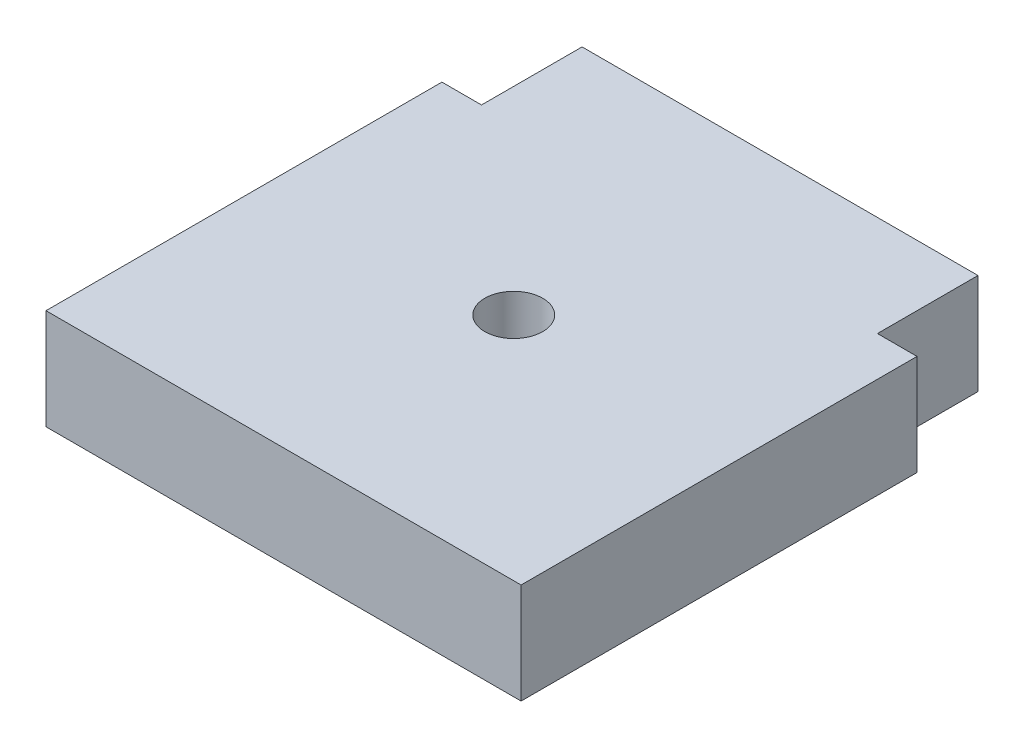
SolidWorks part; units mm, degrees
ref_plane "Front Plane" through (0, 0, 0) normal (0, 0, 1) x (1, 0, 0)
ref_plane "Top Plane" through (0, 0, 0) normal (0, 1, 0) x (1, 0, 0)
ref_plane "Right Plane" through (0, 0, 0) normal (1, 0, 0) x (0, 0, -1)
sketch "Sketch1" plane through (0, 0, 0) normal (0, 1, 0) x (1, 0, 0)
  line L0 (-12.5, 12.5) -> (-15, 12.5)
  line L1 (15, -12.5) -> (-15, -12.5)
  line L2 (15, -12.5) -> (15, 12.5)
  line L3 (15, 12.5) -> (12.5, 12.5)
  line L4 (-15, -12.5) -> (-15, 12.5)
  line L5 (15, -12.5) -> (-15, 12.5) construction
  line L6 (15, 12.5) -> (-15, -12.5) construction
  line L7 (-12.5, 18.85) -> (12.5, 18.85)
  line L8 (-12.5, 18.85) -> (-12.5, 12.5)
  line L10 (12.5, 18.85) -> (12.5, 12.5)
  line L11 (-12.5, 18.85) -> (12.5, 12.5) construction
  line L12 (-12.5, 12.5) -> (12.5, 18.85) construction
  point P0 (0, 0)
  point P6 (0, 15.675)
  dimension "D1" = 25
  dimension "D2" = 30
  dimension "D3" = 6.35
  dimension "D4" = 25
extrude "Boss-Extrude1" add sketch "Sketch1" along normal blind 6.35
sketch "Sketch2" plane through (0, 6.35, 0) normal (0, 1, 0) x (1, 0, 0)
  line L0 (-12.5, 12.5) -> (-15, 12.5) construction
  point P0 (0, 2.0352)
  dimension "D1" = 10.4648
hole_wizard "#6 Clearance Hole1" positions "3DSketch1" profile "Sketch3" hole size "#6" standard "ANSI Inch" end condition through all
sketch3d "3DSketch1"
  point P0 (0, 6.35, -2.0352)
sketch "Sketch3" plane through (0, 6.35, -2.0352) normal (1, 0, 0) x (0, 0, 1)
  line L0 (0, 0) -> (0, 6.35)
  line L1 (0, 6.35) -> (1.8288, 6.35)
  line L2 (1.8288, 6.35) -> (1.8288, 0)
  line L5 (1.8288, 0) -> (0, 0)
  line L11 (0, -6.35) -> (0, 107.95) construction
  dimension "Thru Hole Dia." = 3.6576
  dimension "Thru Hole Depth" = 6.35
